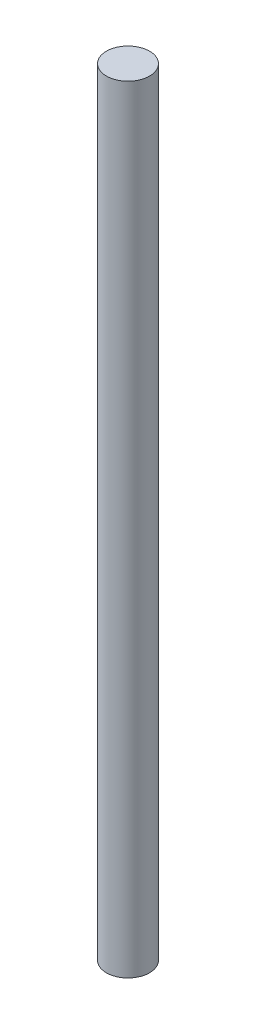
SolidWorks part; units mm, degrees
material "6061 Alloy"
ref_plane "Front Plane" through (0, 0, 0) normal (0, 0, 1) x (1, 0, 0)
ref_plane "Top Plane" through (0, 0, 0) normal (0, 1, 0) x (1, 0, 0)
ref_plane "Right Plane" through (0, 0, 0) normal (1, 0, 0) x (0, 0, -1)
sketch "Sketch1" plane through (0, 0, 0) normal (0, 1, 0) x (1, 0, 0)
  circle A0 centre (0, 0) radius 12.7
  dimension "D1" = 25.4
extrude "Boss-Extrude1" add sketch "Sketch1" along normal blind 457.2
